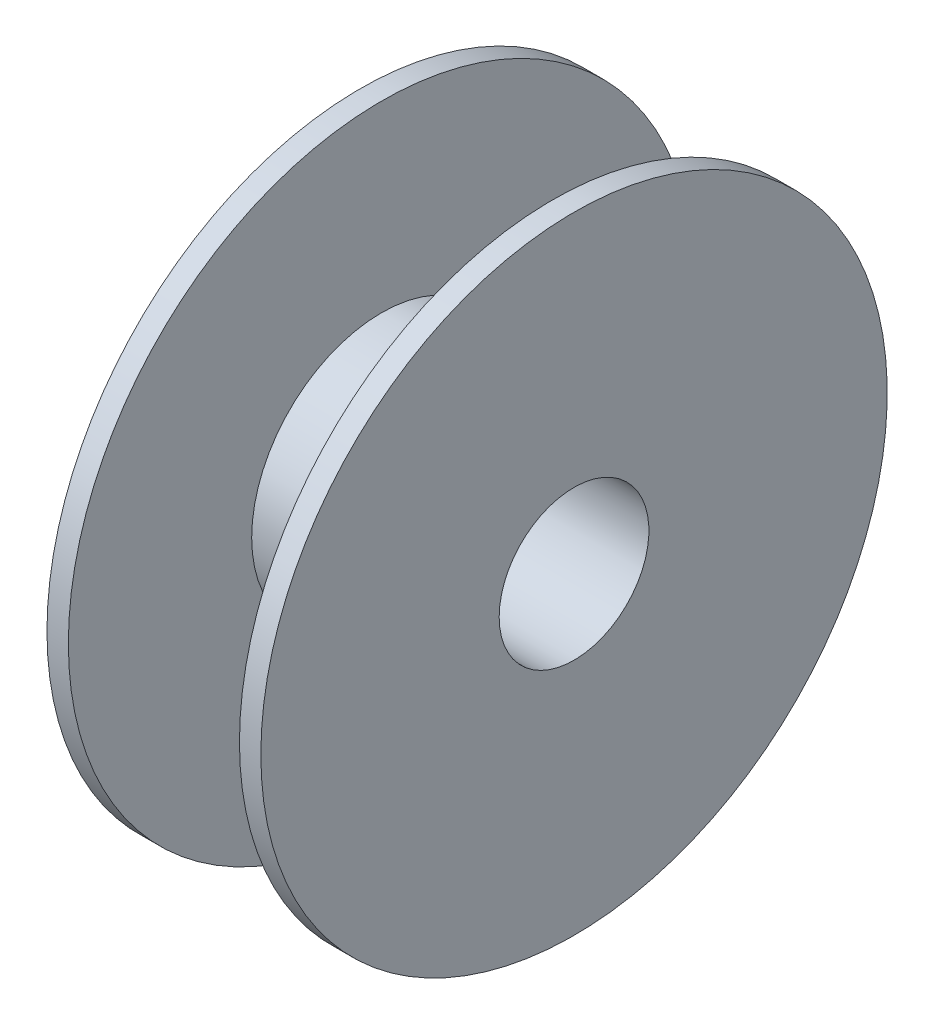
SolidWorks part; units mm, degrees
ref_plane "Frontal" through (0, 0, 0) normal (0, 0, 1) x (1, 0, 0)
ref_plane "Superior" through (0, 0, 0) normal (0, 1, 0) x (1, 0, 0)
ref_plane "Direito" through (0, 0, 0) normal (1, 0, 0) x (0, 0, -1)
sketch "Esboço1" plane through (0, 0, 0) normal (0, 1, 0) x (1, 0, 0)
  line L0 (-72.7317, 0) -> (68.2927, 0) construction
  line L1 (-35, 102.5) -> (-35, 24.5)
  line L2 (-35, 24.5) -> (35, 24.5)
  line L3 (35, 24.5) -> (35, 102.5)
  line L4 (35, 102.5) -> (28, 102.5)
  line L5 (28, 102.5) -> (28, 42.5)
  line L6 (28, 42.5) -> (-28, 42.5)
  line L7 (-28, 42.5) -> (-28, 102.5)
  line L8 (-28, 102.5) -> (-35, 102.5)
  point P5 (0, 24.5)
  point P12 (0, 42.5)
  dimension "D1" = 70
  dimension "D2" = 49
  dimension "D3" = 205
  dimension "D4" = 7
  dimension "D5" = 60
revolve "Revolução1" add sketch "Esboço1" angle 360 about L0
